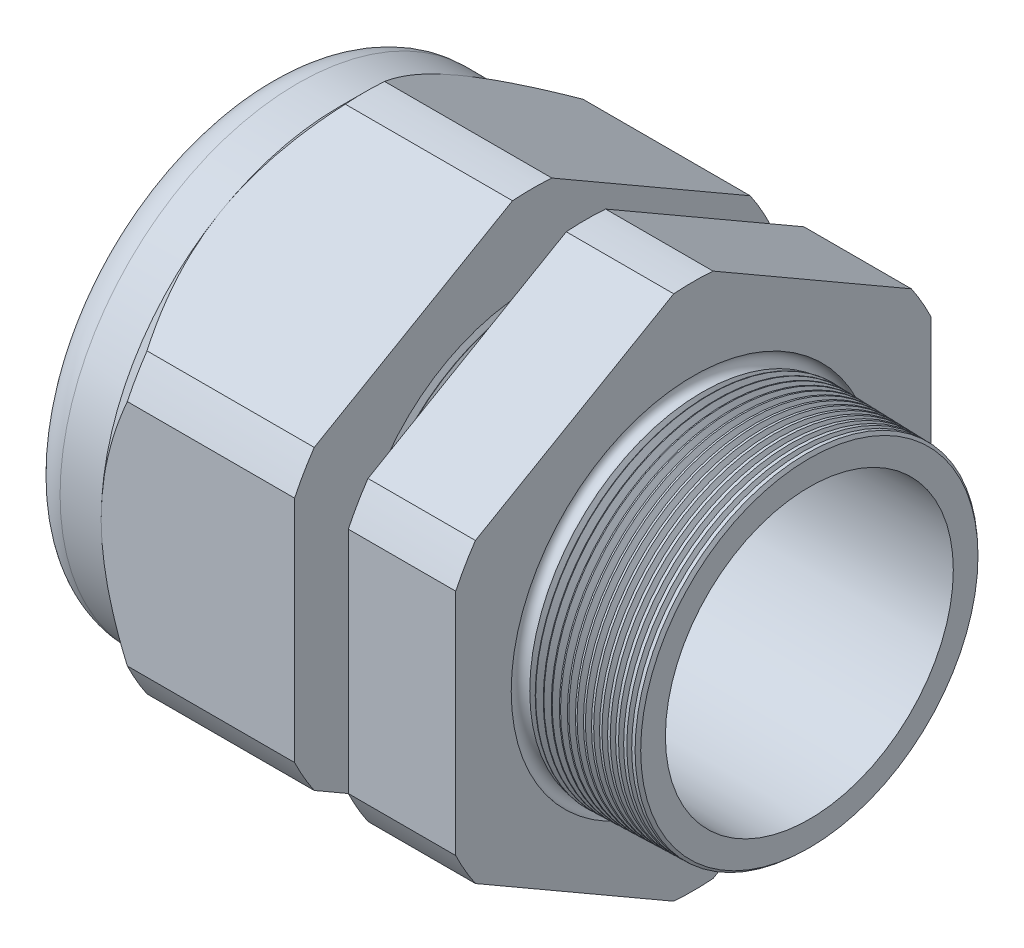
SolidWorks part; units mm, degrees
ref_plane "Front Plane" through (0, 0, 0) normal (0, 0, 1) x (1, 0, 0)
ref_plane "Top Plane" through (0, 0, 0) normal (0, 1, 0) x (1, 0, 0)
ref_plane "Right Plane" through (0, 0, 0) normal (1, 0, 0) x (0, 0, -1)
sketch "Sketch10" plane through (0, 0, 0) normal (0, 0, 1) x (1, 0, 0)
  line L0 (0, 0) -> (-115.3565, 0) construction
  line L1 (-55.88, 16.002) -> (-25.8776, 16.002)
  line L2 (5.08, 16.0803) -> (5.08, 19.1283)
  line L3 (-7.874, 19.4676) -> (5.08, 19.1283)
  line L4 (-7.874, 53.086) -> (-7.874, 19.4676)
  line L5 (-7.874, 53.086) -> (-19.874, 53.086)
  line L6 (-19.874, 53.086) -> (-19.874, 19.7818)
  line L7 (-25.8776, 19.939) -> (-19.874, 19.7818)
  line L8 (-25.8776, 19.939) -> (-25.8776, 53.086)
  line L9 (-25.8776, 53.086) -> (-47.48, 53.086)
  line L10 (-47.48, 53.086) -> (-47.48, 26.543)
  line L11 (-47.48, 26.543) -> (-55.88, 26.543)
  line L12 (-55.88, 26.543) -> (-55.88, 16.002)
  line L13 (-25.8776, 16.002) -> (5.08, 16.0803)
  dimension "D1" = 60.96
  dimension "D2" = 32.004
  dimension "D3" = 1.5
  dimension "D4" = 3.048
  dimension "A" = 39.878
  dimension "D6" = 53.086
  dimension "D8" = 106.172
  dimension "D9" = 8.4
  dimension "D10" = 21.6024
  dimension "D11" = 12
  dimension "D" = 12.954
revolve "Revolve2" add sketch "Sketch10" angle 360 about L0
sketch "Sketch12" plane through (-47.48, 0, 0) normal (-1, 0, 0) x (0, 0, 1)
  line L1 (-2.1972, 29.3807) -> (-24.3458, 16.5931)
  line L2 (-26.543, 12.7876) -> (-26.543, -12.7876)
  line L3 (-24.3458, -16.5931) -> (-2.1972, -29.3807)
  line L4 (2.1972, -29.3807) -> (24.3458, -16.5931)
  line L5 (26.543, -12.7876) -> (26.543, 12.7876)
  line L6 (24.3458, 16.5931) -> (2.1972, 29.3807)
  circle A0 centre (0, 0) radius 26.543 construction
  arc A1 (2.1972, 29.3807) -> (-2.1972, 29.3807) centre (0, 0) ccw
  arc A2 (-24.3458, 16.5931) -> (-26.543, 12.7876) centre (0, 0) ccw
  arc A3 (-26.543, -12.7876) -> (-24.3458, -16.5931) centre (0, 0) ccw
  arc A4 (-2.1972, -29.3807) -> (2.1972, -29.3807) centre (0, 0) ccw
  arc A5 (24.3458, -16.5931) -> (26.543, -12.7876) centre (0, 0) ccw
  arc A6 (26.543, 12.7876) -> (24.3458, 16.5931) centre (0, 0) ccw
  dimension "D2" = 58.9255
  dimension "D1" = 53.086
extrude "Cut-Extrude2" cut sketch "Sketch12" against normal through all flip side to cut
fillet "Fillet4" radius 3.81 1 edges at (-55.88, 0, -26.543)
sketch "Sketch19" plane through (-47.48, 0, 0) normal (-1, 0, 0) x (0, 0, 1)
  line L0 (26.543, 0) -> (26.543, 12.7876) construction
  circle A0 centre (0, 0) radius 26.543
extrude "Cut-Extrude3" cut sketch "Sketch19" against normal blind 3.998 draft 45 flip side to cut
chamfer "Chamfer1" distance 0.254 angle 45 1 edges at (5.08, 0, -19.1283)
sketch "Sketch21" plane through (-55.88, 0, 0) normal (-1, 0, 0) x (0, 0, 1)
  circle A0 centre (0, 0) radius 16.002
  circle A2 centre (0, 0) radius 16.002 construction
extrude "plug" add sketch "Sketch21" against normal blind 12.7 separate body
sketch "Sketch22" plane through (-55.88, 0, 0) normal (-1, 0, 0) x (0, 0, 1)
  circle A0 centre (0, 0) radius 15.748
  circle A1 centre (0, 0) radius 16.002 construction
  dimension "D1" = 0.254
extrude "Cut-Extrude4" cut sketch "Sketch22" against normal blind 0.508
sketch "Sketch27" plane through (-55.372, 0, 0) normal (-1, 0, 0) x (0, 0, 1)
  line L0 (-4.3624, 0) -> (4.3624, 0) construction
  circle A0 centre (-8.225, 0) radius 7.493
  circle A1 centre (0, 0) radius 15.748 construction
  dimension "D1" = 0.03
  dimension "holedia" = 14.986
extrude "plugholes" cut sketch "Sketch27" against normal through all
pattern_circular "CirPattern1" count 2 over 360 about axis through (0, 0, 0) along (1, 0, 0) of "plugholes"
sketch "Sketch28" [suppressed] plane through (-29.464, 0, 0) normal (-1, 0, 0) x (0, 0, 1)
  circle A0 centre (0, 0) radius 0.762
  dimension "midholedia" = 14.986
extrude "midhole" [suppressed] cut sketch "Sketch28" against normal through all
sketch "Sketch29" plane through (0, 0, 0) normal (0, 0, 1) x (1, 0, 0)
  line L0 (-25.8776, 19.939) -> (-25.1446, 19.9198)
  line L1 (-19.874, 19.7818) -> (-25.8776, 19.939) construction
  line L2 (-25.1446, 19.9198) -> (-25.5277, 19.2946)
  line L3 (-25.5277, 19.2946) -> (-25.8776, 19.939)
  dimension "D1" = 60
  dimension "D2" = 60
  dimension "D3" = 0.635
revolve "Cut-Revolve1" cut sketch "Sketch29" angle 360 about axis through (0, 0, 0) along (-1, 0, 0)
pattern_linear "LPattern1" count 8 spacing 0.762 along (1, 0, 0) of "Cut-Revolve1"
sketch "Sketch30" plane through (0, 0, 0) normal (0, 0, 1) x (1, 0, 0)
  line L0 (-7.874, 19.4676) -> (-6.9944, 19.4445)
  line L1 (-7.874, 29.3807) -> (-7.874, 16.5931) construction
  line L2 (4.8261, 19.135) -> (-7.874, 19.4676) construction
  line L3 (-6.9944, 19.4445) -> (-7.4542, 18.6943)
  line L4 (-7.4542, 18.6943) -> (-7.874, 19.4676)
  dimension "D1" = 60
  dimension "D2" = 60
  dimension "D3" = 0.762
revolve "Cut-Revolve2" cut sketch "Sketch30" angle 360 about axis through (0, 0, 0) along (-1, 0, 0)
pattern_linear "LPattern2" count 15 spacing 0.889 along (1, 0, 0) of "Cut-Revolve2"
sketch "Sketch31" [suppressed] plane through (-38.354, 0, 0) normal (-1, 0, 0) x (0, 0, 1)
  line L0 (-1.905, 1.905) -> (1.905, 1.905)
  line L1 (-1.905, -1.905) -> (1.905, -1.905)
  circle A0 centre (0, 0) radius 1.905 construction
  arc A1 (-1.905, 1.905) -> (-1.905, -1.905) centre (-1.905, 0) ccw
  arc A2 (1.905, 1.905) -> (1.905, -1.905) centre (1.905, 0) cw
extrude "Cut-Extrude5" [suppressed] cut sketch "Sketch31" against normal through all
sketch "Sketch32" plane through (0, 0, 0) normal (0, 0, 1) x (1, 0, 0)
  line L0 (-7.874, 29.3807) -> (-7.874, 16.5931) construction
  circle A0 centre (-7.747, 19.4676) radius 0.889
  dimension "D2" = 1.778
  dimension "D1" = 0.127
revolve "Cut-Revolve3" cut sketch "Sketch32" angle 360 about axis through (0, 0, 0) along (-1, 0, 0)
